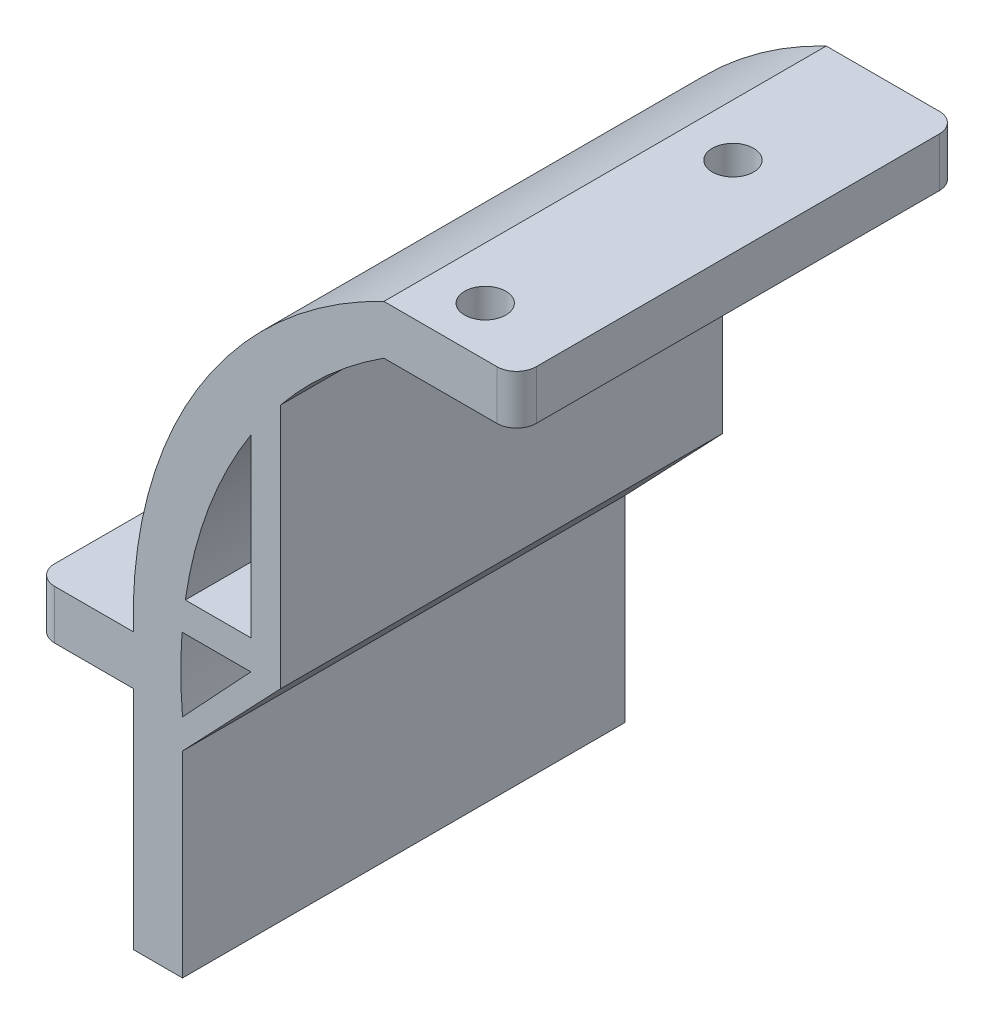
SolidWorks part; units mm, degrees
ref_plane "Front Plane" through (0, 0, 0) normal (0, 0, 1) x (1, 0, 0)
ref_plane "Top Plane" through (0, 0, 0) normal (0, 1, 0) x (1, 0, 0)
ref_plane "Right Plane" through (0, 0, 0) normal (1, 0, 0) x (0, 0, -1)
sketch "Sketch3" plane through (0, 0, 0) normal (0, 0, 1) x (1, 0, 0)
  line L5 (8.4348, 262.2647) -> (-5.0652, 262.2647)
  line L6 (8.4348, 262.2647) -> (8.4348, 257.2647)
  line L7 (8.4348, 257.2647) -> (-5.0652, 257.2647)
  line L8 (-5.0652, 262.2647) -> (-5.0652, 257.2647)
  line L9 (-40.5516, 215.4144) -> (-30.5516, 215.4144)
  line L10 (-40.5516, 215.4144) -> (-40.5516, 220.4144)
  line L11 (-40.5516, 220.4144) -> (-30.5516, 220.4144)
  line L12 (-30.5516, 215.4144) -> (-30.5516, 220.4144)
  line L13 (-30.5516, 215.4144) -> (-25.5516, 215.4144)
  line L14 (-30.5516, 215.4144) -> (-30.5516, 192.4144)
  line L15 (-30.5516, 192.4144) -> (-25.5516, 192.4144)
  line L16 (-25.5516, 215.4144) -> (-25.5516, 192.4144)
  arc A0 (-30.5516, 220.4144) -> (-5.0652, 262.2647) centre (14.4298, 221.7068) cw
  arc A1 (-5.0652, 257.2647) -> (-25.5516, 215.4144) centre (19.2704, 219.4126) ccw
  dimension "D8" = 45
  dimension "D9" = 45
  dimension "D3" = 13.5
  dimension "D4" = 5
  dimension "D6" = 10
  dimension "D7" = 5
extrude "Boss-Extrude1" add sketch "Sketch3" along normal blind 45 contours A1 L8 A0 L12 L13 | L5 L8 L7 L6 | L9 L12 L11 L10 | L16 L13 L14 L15
fillet "Fillet1" radius 2 4 edges at (-40.5516, 217.9144, 45) (-40.5516, 217.9144, 0) (8.4348, 259.7647, 0) (8.4348, 259.7647, 45)
sketch "Sketch5" plane through (0, 262.2647, 0) normal (0, 1, 0) x (1, 0, 0)
  line L0 (-5.0652, -45) -> (-5.0652, 0) construction
  line L2 (6.4348, -45) -> (-5.0652, -45) construction
  circle A0 centre (0.2448, -40) radius 2.1
  circle A2 centre (0.2448, -14.8) radius 2.1
  dimension "D1" = 5.31
  dimension "D2" = 4.2
  dimension "D4" = 5
  dimension "D6" = 4.2
extrude "Cut-Extrude2" cut sketch "Sketch5" against normal blind 45
sketch "Sketch6" plane through (0, 220.4144, 0) normal (0, 1, 0) x (1, 0, 0)
  line L0 (-38.5516, -45) -> (-30.5516, -45) construction
  line L1 (-40.5516, -43) -> (-40.5516, -2) construction
  line L2 (-38.5516, 0) -> (-30.5516, 0) construction
  circle A0 centre (-35.5516, -10) radius 2.1
  circle A1 centre (-35.5516, -35) radius 2.1
  dimension "D1" = 4.2
  dimension "D2" = 4.2
  dimension "D3" = 10
  dimension "D4" = 5
  dimension "D5" = 5
  dimension "D6" = 10
extrude "Cut-Extrude3" cut sketch "Sketch6" against normal blind 45
sketch "Sketch7" plane through (0, 0, 45) normal (0, 0, 1) x (1, 0, 0)
  line L0 (-15.5974, 247.8598) -> (-15.5974, 222.8598)
  line L1 (-15.5974, 222.8598) -> (-25.5974, 222.8598)
  line L2 (-18.5974, 243.7238) -> (-18.5974, 225.8598)
  line L3 (-18.5974, 225.8598) -> (-25.2654, 225.8598)
  arc A0 (-5.0652, 257.2647) -> (-25.5516, 215.4144) centre (19.2704, 219.4126) ccw construction
  arc A1 (-15.5974, 247.8598) -> (-18.5974, 243.7238) centre (19.2704, 219.4126) ccw
  arc A2 (-25.2654, 225.8598) -> (-25.5974, 222.8598) centre (19.2704, 219.4126) ccw
  dimension "D1" = 10
  dimension "D2" = 25
  dimension "D3" = 3
  dimension "D4" = 3
extrude "Boss-Extrude3" add sketch "Sketch7" against normal through all
sketch "Sketch8" plane through (0, 0, 45) normal (0, 0, 1) x (1, 0, 0)
  line L0 (-15.5974, 222.8598) -> (-25.5516, 212.4144)
  line L1 (-25.5516, 215.4144) -> (-25.5516, 192.4144) construction
  line L2 (-18.5974, 222.8598) -> (-25.5516, 215.4144)
  line L3 (-25.5974, 222.8598) -> (-15.5974, 222.8598) construction
  line L4 (-25.5516, 215.4144) -> (-25.5516, 212.4144)
  line L5 (-18.5974, 222.8598) -> (-15.5974, 222.8598)
  dimension "D1" = 3
  dimension "D2" = 3
extrude "Boss-Extrude4" add sketch "Sketch8" against normal through all
